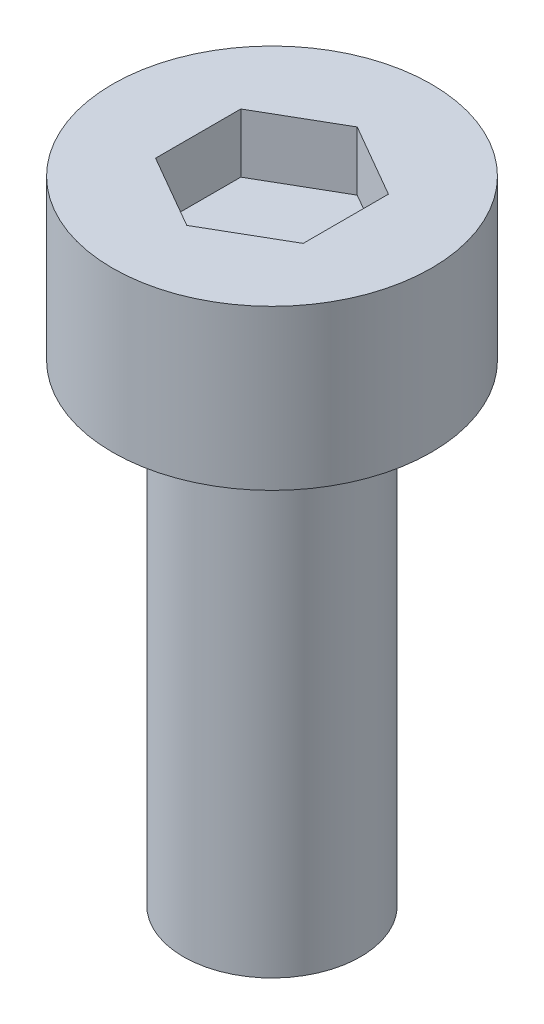
SolidWorks part; units mm, degrees
ref_plane "Front Plane" through (0, 0, 0) normal (0, 0, 1) x (1, 0, 0)
ref_plane "Top Plane" through (0, 0, 0) normal (0, 1, 0) x (1, 0, 0)
ref_plane "Right Plane" through (0, 0, 0) normal (1, 0, 0) x (0, 0, -1)
sketch "Sketch1" plane through (0, 0, 0) normal (0, 1, 0) x (1, 0, 0)
  circle A0 centre (0, 0) radius 2.7
extrude "Boss-Extrude1" add sketch "Sketch1" along normal blind 2.7
sketch "Sketch2" plane through (0, 2.7, 0) normal (0, 1, 0) x (1, 0, 0)
  line L1 (0, 1.4434) -> (-1.25, 0.7217)
  line L2 (-1.25, 0.7217) -> (-1.25, -0.7217)
  line L3 (-1.25, -0.7217) -> (0, -1.4434)
  line L4 (0, -1.4434) -> (1.25, -0.7217)
  line L5 (1.25, -0.7217) -> (1.25, 0.7217)
  line L6 (1.25, 0.7217) -> (0, 1.4434)
  circle A0 centre (0, 0) radius 1.25 construction
extrude "Cut-Extrude1" cut sketch "Sketch2" against normal blind 1
sketch "Sketch3" plane through (0, 0, 0) normal (0, -1, 0) x (1, 0, 0)
  circle A0 centre (0, 0) radius 1.5
extrude "Boss-Extrude2" add sketch "Sketch3" along normal blind 8
